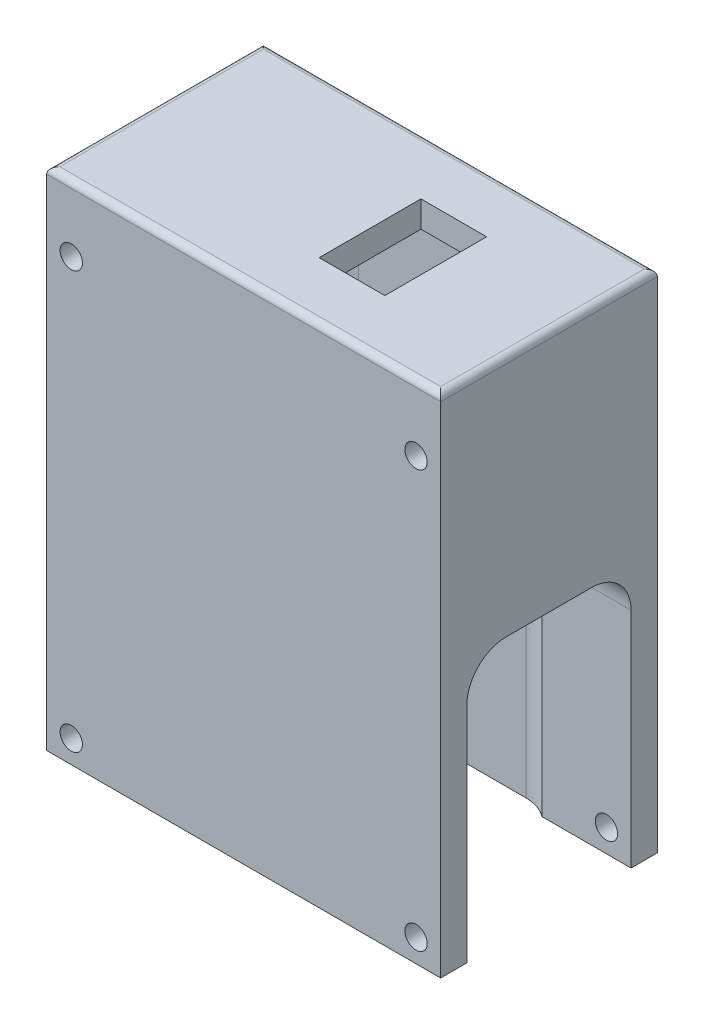
SolidWorks part; units mm, degrees
material "ABS"
ref_plane "Front" through (0, 0, 0) normal (0, 0, 1) x (1, 0, 0)
ref_plane "Top" through (0, 0, 0) normal (0, 1, 0) x (1, 0, 0)
ref_plane "Right" through (0, 0, 0) normal (1, 0, 0) x (0, 0, -1)
sketch "ｽｹｯﾁ1" plane through (0, 0, 0) normal (0, 1, 0) x (1, 0, 0)
  line L1 (30, 16.5) -> (-30, 16.5)
  line L2 (30, 16.5) -> (30, -16.5)
  line L3 (30, -16.5) -> (-30, -16.5)
  line L4 (-30, 16.5) -> (-30, -16.5)
  line L5 (30, 16.5) -> (-30, -16.5) construction
  line L6 (30, -16.5) -> (-30, 16.5) construction
  point P0 (0, 0)
  dimension "D1" = 33
  dimension "D2" = 60
extrude "ﾎﾞｽ - 押し出し1" add sketch "ｽｹｯﾁ1" along normal blind 77
sketch "ｽｹｯﾁ2" plane through (0, 0, 0) normal (0, -1, 0) x (1, 0, 0)
  line L1 (12.75, 13.75) -> (-12.75, 13.75)
  line L2 (18.75, 7.75) -> (18.75, -7.75)
  line L3 (12.75, -13.75) -> (-12.75, -13.75)
  line L4 (-18.75, 7.75) -> (-18.75, -7.75)
  line L5 (18.75, 13.75) -> (-18.75, -13.75) construction
  line L6 (18.75, -13.75) -> (-18.75, 13.75) construction
  arc A0 (12.75, 13.75) -> (18.75, 7.75) centre (12.75, 7.75) cw
  arc A1 (18.75, -7.75) -> (12.75, -13.75) centre (12.75, -7.75) cw
  arc A2 (-12.75, -13.75) -> (-18.75, -7.75) centre (-12.75, -7.75) cw
  arc A3 (-18.75, 7.75) -> (-12.75, 13.75) centre (-12.75, 7.75) cw
  point P0 (0, 0)
  dimension "D3" = 6
  dimension "D1" = 37.5
  dimension "D2" = 27.5
extrude "ｶｯﾄ - 押し出し1" cut sketch "ｽｹｯﾁ2" against normal blind 73
sketch "ｽｹｯﾁ3" plane through (0, 0, 16.5) normal (0, 0, 1) x (1, 0, 0)
  line L0 (-30, 0) -> (30, 0) construction
  line L1 (-30, 77) -> (-30, 0) construction
  line L2 (-30, 77) -> (30, 77) construction
  line L3 (30, 77) -> (30, 0) construction
  circle A0 centre (26.25, 3.5) radius 1.7
  circle A1 centre (26.25, 67) radius 1.7
  circle A2 centre (-26.25, 67) radius 1.7
  circle A3 centre (-26.25, 3.5) radius 1.7
  dimension "D1" = 3.4
  dimension "D2" = 3.5
  dimension "D3" = 3.75
  dimension "D4" = 10
  dimension "D5" = 3.75
extrude "ｶｯﾄ - 押し出し2" cut sketch "ｽｹｯﾁ3" against normal through all
sketch "ｽｹｯﾁ4" plane through (-30, 0, 0) normal (-1, 0, 0) x (0, 0, 1)
  line L0 (-16.5, 0) -> (16.5, 0) construction
  line L1 (6.5, 40) -> (-6.5, 40)
  line L2 (12.5, 34) -> (12.5, 0)
  line L3 (12.5, 0) -> (-12.5, 0)
  line L4 (-12.5, 34) -> (-12.5, 0)
  line L5 (12.5, 40) -> (-12.5, 0) construction
  line L6 (12.5, 0) -> (-12.5, 40) construction
  arc A0 (6.5, 40) -> (12.5, 34) centre (6.5, 34) cw
  arc A1 (-6.5, 40) -> (-12.5, 34) centre (-6.5, 34) ccw
  point P0 (0, 20)
  dimension "D4" = 6
  dimension "D1" = 25
  dimension "D2" = 40
  dimension "D3" = 0
extrude "ｶｯﾄ - 押し出し3" cut sketch "ｽｹｯﾁ4" against normal through all
sketch "ｽｹｯﾁ5" plane through (0, 73, 0) normal (0, -1, 0) x (1, 0, 0)
  line L0 (18.75, -7.75) -> (18.75, 7.75) construction
  line L1 (2.75, -7.75) -> (12.75, -7.75)
  line L2 (2.75, -7.75) -> (2.75, 7.75)
  line L3 (2.75, 7.75) -> (12.75, 7.75)
  line L4 (12.75, -7.75) -> (12.75, 7.75)
  line L5 (2.75, -7.75) -> (12.75, 7.75) construction
  line L6 (2.75, 7.75) -> (12.75, -7.75) construction
  line L7 (-12.75, -13.75) -> (12.75, -13.75) construction
  line L8 (12.75, 13.75) -> (-12.75, 13.75) construction
  point P0 (7.75, 0)
  dimension "D1" = 6
  dimension "D2" = 6
  dimension "D3" = 6
  dimension "D4" = 10
extrude "ｶｯﾄ - 押し出し4" cut sketch "ｽｹｯﾁ5" against normal through all
fillet "ﾌｨﾚｯﾄ1" radius 1 4 edges at (0, 77, 16.5) (-30, 77, 0) (0, 77, -16.5) (30, 77, 0)
